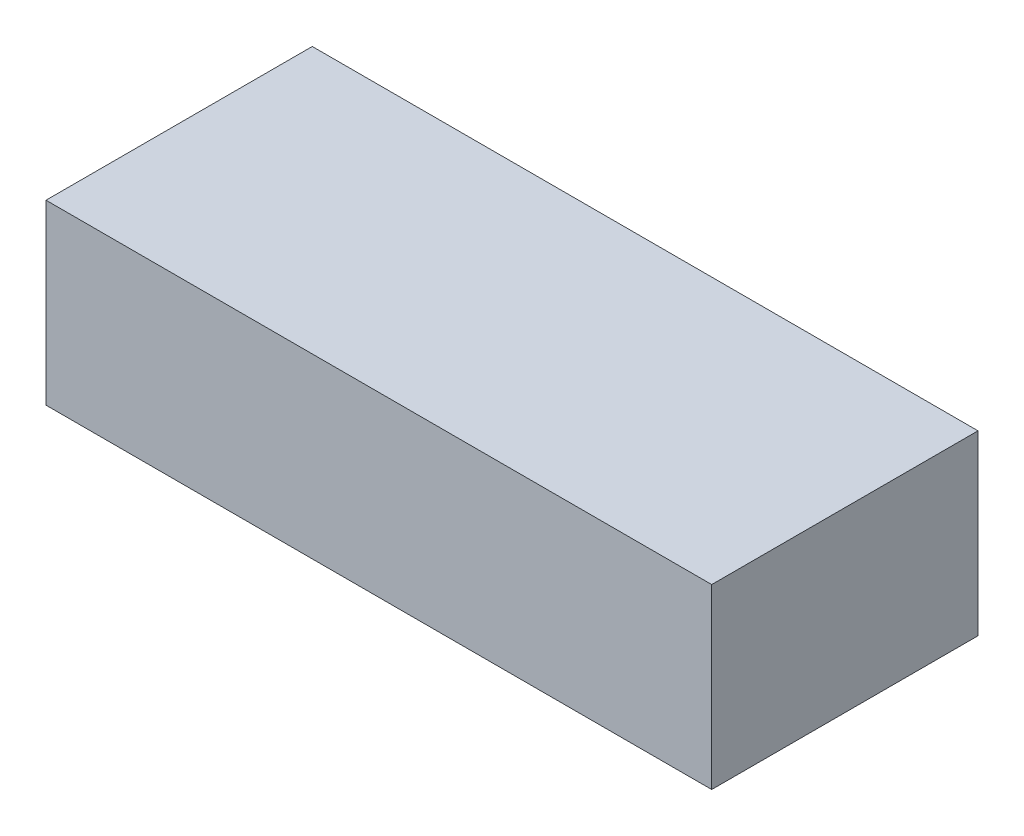
SolidWorks part; units mm, degrees
ref_plane "Front Plane" through (0, 0, 0) normal (0, 0, 1) x (1, 0, 0)
ref_plane "Top Plane" through (0, 0, 0) normal (0, 1, 0) x (1, 0, 0)
ref_plane "Right Plane" through (0, 0, 0) normal (1, 0, 0) x (0, 0, -1)
sketch "Sketch1" plane through (0, 0, 0) normal (0, 1, 0) x (1, 0, 0)
  line L1 (0, 0) -> (-150, 0)
  line L2 (0, 0) -> (0, -60)
  line L3 (0, -60) -> (-150, -60)
  line L4 (-150, 0) -> (-150, -60)
  dimension "D1" = 150
  dimension "D2" = 60
extrude "Boss-Extrude1" add sketch "Sketch1" along normal blind 40
